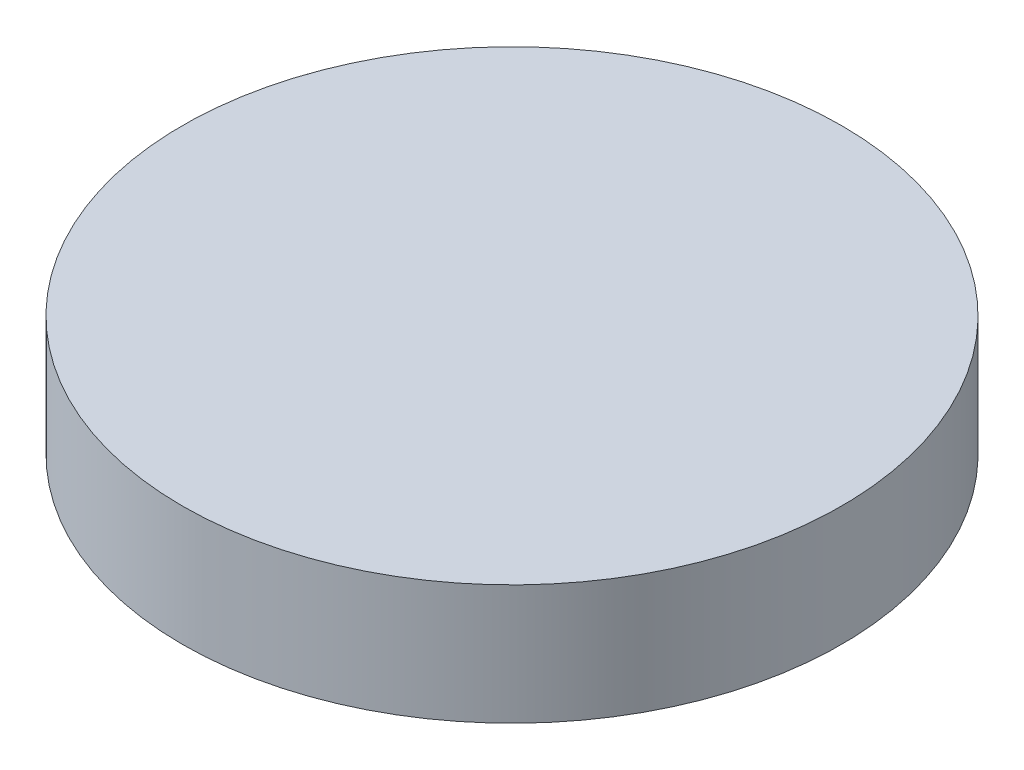
SolidWorks part; units mm, degrees
ref_plane "前视基准面" through (0, 0, 0) normal (0, 0, 1) x (1, 0, 0)
ref_plane "上视基准面" through (0, 0, 0) normal (0, 1, 0) x (1, 0, 0)
ref_plane "右视基准面" through (0, 0, 0) normal (1, 0, 0) x (0, 0, -1)
sketch "草图1" plane through (0, 0, 0) normal (0, 1, 0) x (1, 0, 0)
  circle A0 centre (0, 0) radius 8.25
  dimension "D1" = 16.5
extrude "凸台-拉伸1" add sketch "草图1" along normal blind 3
